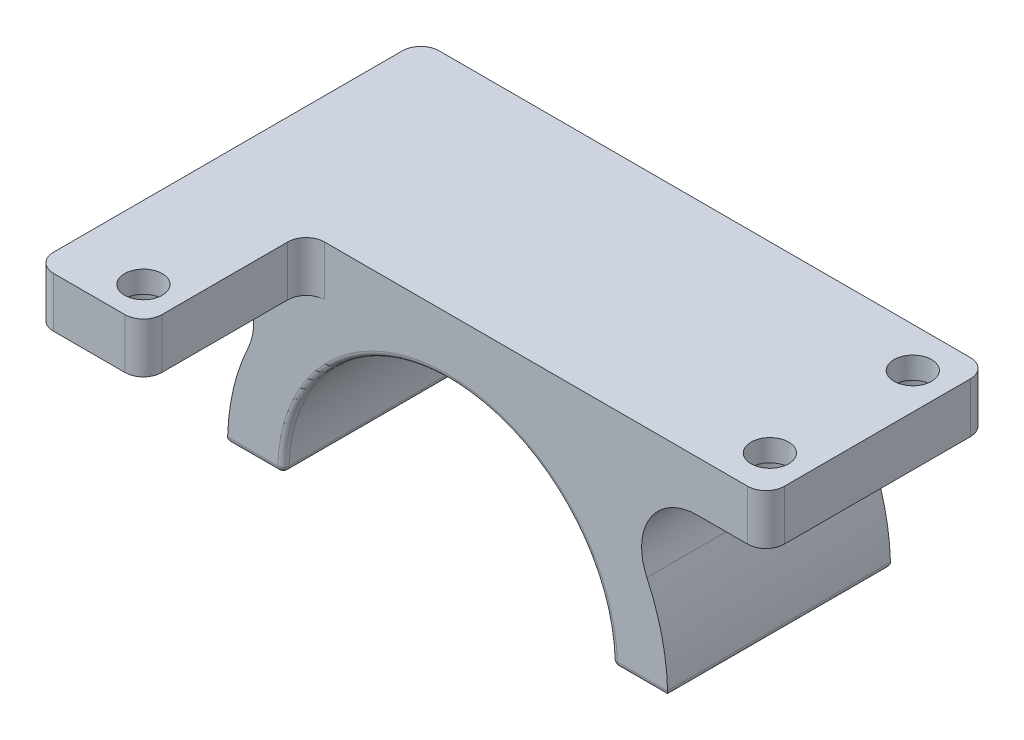
SolidWorks part; units mm, degrees
ref_plane "Front Plane" through (0, 0, 0) normal (0, 0, 1) x (1, 0, 0)
ref_plane "Top Plane" through (0, 0, 0) normal (0, 1, 0) x (1, 0, 0)
ref_plane "Right Plane" through (0, 0, 0) normal (1, 0, 0) x (0, 0, -1)
sketch "Sketch1" plane through (0, 0, 0) normal (0, 0, 1) x (1, 0, 0)
  circle A0 centre (0, 0) radius 39.5
  dimension "D1" = 79
extrude "Boss-Extrude1" add sketch "Sketch1" along normal blind 40 contours A0
sketch "Sketch2" plane through (0, 0, 0) normal (0, 0, -1) x (-1, 0, 0)
  line L0 (-39.5, 0) -> (39.5, 0)
  circle A0 centre (0, 0) radius 39.5 construction
  arc A2 (39.5, 0) -> (-39.5, 0) centre (0, 0) cw
extrude "Cut-Extrude2" cut sketch "Sketch2" against normal through all contours A2 L0
sketch "Sketch3" plane through (0, 0, 0) normal (0, 0, -1) x (-1, 0, 0)
  line L0 (-39.5, 0) -> (39.5, 0) construction
  line L1 (-29.5, 0) -> (29.5, 0)
  arc A0 (-29.5, 0) -> (29.5, 0) centre (0, 0) cw
  dimension "D1" = 29.5
extrude "Cut-Extrude3" cut sketch "Sketch3" against normal through all
fillet "Fillet2" radius 1 10 edges at (29.5, 0, 20) (-29.5, 0, 20) (0, 29.5, 40) (0, 29.5, 0) (-39.5, 0, 20) (39.5, 0, 20) (34.5, 0, 40) (-34.5, 0, 40) (34.5, 0, 0) (-34.5, 0, 0)
sketch "Sketch6" plane through (0, 0, 0) normal (0, 0, -1) x (-1, 0, 0)
  line L5 (-57.15, 40) -> (57.15, 40)
  line L6 (-57.15, 40) -> (-57.15, 31)
  line L7 (-57.15, 31) -> (57.15, 31)
  line L8 (57.15, 40) -> (57.15, 31)
  arc A0 (39.4867, 1.026) -> (-39.4867, 1.026) centre (0, 0) ccw construction
  point P9 (0, 39.5)
  point P10 (0, 31)
  dimension "D3" = 40
  dimension "D1" = 9
  dimension "D2" = 114.3
extrude "Boss-Extrude2" add sketch "Sketch6" against normal up to surface (40 mm away) up to face at (0, 12.3377, 40)
fillet "Fillet6" radius 10 2 edges at (-24.4796, 31, 20) (24.4796, 31, 20)
ref_plane "Plane1" through (-44.8247, 31, 0) normal (-1, 0, 0) x (0, 0, 1)
sketch "Sketch9" plane through (0, 40, 0) normal (0, 1, 0) x (1, 0, 0)
  line L1 (-50.6774, -7.173) -> (-50.6774, -3.7948) construction
  line L4 (-57.15, -40) -> (-57.15, 0) construction
  line L5 (-50.6774, -7.173) -> (-50.6774, -32.827) construction
  circle A0 centre (-50.6774, -7.173) radius 3.3782
  circle A1 centre (-50.6774, -32.827) radius 3.3782
  point P5 (-50.6774, -20)
  point P6 (-57.15, -20)
  dimension "D1" = 6.7564
  dimension "D2" = 6.4726
  dimension "D3" = 2
extrude "Cut-Extrude4" cut sketch "Sketch9" against normal up to surface (10.8916 mm away)
sketch "Sketch10" plane through (0, 40, 0) normal (0, 1, 0) x (1, 0, 0)
  line L0 (57.15, -40) -> (57.15, 0) construction
  circle A0 centre (50.8, -23.937) radius 3.3782
  circle A1 centre (50.8, -61.529) radius 3.3782
  circle A3 centre (-50.6774, -7.173) radius 3.3782 construction
  dimension "D1" = 6.7564
  dimension "D3" = 16.764
  dimension "D4" = 6.35
  dimension "D2" = 2
sketch "Sketch11" plane through (0, 0, 40) normal (0, 0, 1) x (1, 0, 0)
  line L0 (-57.15, 40) -> (57.15, 40) construction
  line L1 (25.4, 40) -> (57.15, 40)
  line L2 (25.4, 40) -> (25.4, 31)
  line L3 (25.4, 31) -> (57.15, 31)
  line L4 (57.15, 40) -> (57.15, 31)
  dimension "D1" = 31.75
extrude "Boss-Extrude3" add sketch "Sketch11" along normal blind 29.21
sketch "Sketch12" plane through (0, 40, 0) normal (0, 1, 0) x (1, 0, 0)
  circle A0 centre (50.8, -23.937) radius 3.3782 construction
  circle A1 centre (50.8, -23.937) radius 3.3782
  circle A2 centre (50.8, -61.529) radius 3.3782 construction
  circle A3 centre (50.8, -61.529) radius 3.3782
sketch "Sketch4" plane through (0, 0, 0) normal (0, -1, 0) x (1, 0, 0)
  line L0 (38.487, 40) -> (30.5, 40) construction
  line L1 (32.9841, 35) -> (35.987, 35)
  line L2 (32.9841, 35) -> (32.9841, 5)
  line L3 (32.9841, 5) -> (35.987, 5)
  line L4 (35.987, 35) -> (35.987, 5)
  line L5 (38.487, 0) -> (-30.5, 0) construction
  line L7 (39.487, 0) -> (39.487, 40) construction
  line L8 (29.4841, 1) -> (29.4841, 39) construction
  line L9 (0, 0) -> (0, 64.0682) construction
  dimension "D1" = 5
  dimension "D2" = 5
  dimension "D3" = 3.5
  dimension "D4" = 3.5
revolve "Cut-Revolve1" cut sketch "Sketch4" angle 360 about L9
fillet "Fillet7" radius 3.302 6 edges at (-57.15, 35.5, 40) (-57.15, 35.5, 0) (57.15, 35.5, 0) (57.15, 35.5, 69.21) (25.4, 35.5, 69.21) (25.4, 35.5, 40)
sketch "Sketch13" plane through (0, 31, 0) normal (0, -1, 0) x (1, 0, 0)
  circle A0 centre (-50.6774, 32.827) radius 5.08
  circle A1 centre (-50.6774, 32.827) radius 3.3782 construction
  circle A2 centre (-50.6774, 7.173) radius 5.08
  dimension "D1" = 10.16
  dimension "D2" = 2
extrude "Cut-Extrude6" cut sketch "Sketch13" against normal blind 5.08
sketch "Sketch14" plane through (0, 31, 0) normal (0, -1, 0) x (1, 0, 0)
  circle A0 centre (50.8, 61.529) radius 5.08
  circle A1 centre (50.8, 24.191) radius 5.08
  dimension "D1" = 10.16
  dimension "D2" = 2
sketch "Sketch15" plane through (0, 31, 0) normal (0, -1, 0) x (1, 0, 0)
  line L0 (25.4, 65.908) -> (25.4, 43.302) construction
  line L2 (28.702, 69.21) -> (53.848, 69.21) construction
  circle A0 centre (31.75, 62.86) radius 3.3782
  dimension "D1" = 6.7564
  dimension "D2" = 6.35
  dimension "D3" = 6.35
extrude "Cut-Extrude8" cut sketch "Sketch15" against normal through all
sketch "Sketch16" plane through (0, 31, 0) normal (0, -1, 0) x (1, 0, 0)
  circle A0 centre (31.75, 62.86) radius 5.08
  circle A1 centre (31.75, 62.86) radius 3.3782 construction
  dimension "D1" = 10.16
extrude "Cut-Extrude9" cut sketch "Sketch16" against normal blind 5.08
sketch "Sketch17" plane through (0, 31, 0) normal (0, -1, 0) x (1, 0, 0)
  line L1 (44.8247, 0) -> (81.4109, 0)
  line L2 (44.8247, 0) -> (44.8247, 70.8356)
  line L3 (44.8247, 70.8356) -> (81.4109, 70.8356)
  line L4 (81.4109, 0) -> (81.4109, 70.8356)
extrude "Cut-Extrude10" cut sketch "Sketch17" against normal through all
fillet "Fillet8" radius 3.302 2 edges at (44.8247, 35.5, 69.21) (44.8247, 35.5, 0)
mirror "Mirror7" [suppressed]
mirror "Mirror8" about plane through (-57.15, 40, 154.6538) normal (-1, 0, 0) of bodies 116
delete or keep bodies "Body-Delete/Keep 3" type delete bodies bodies 116
